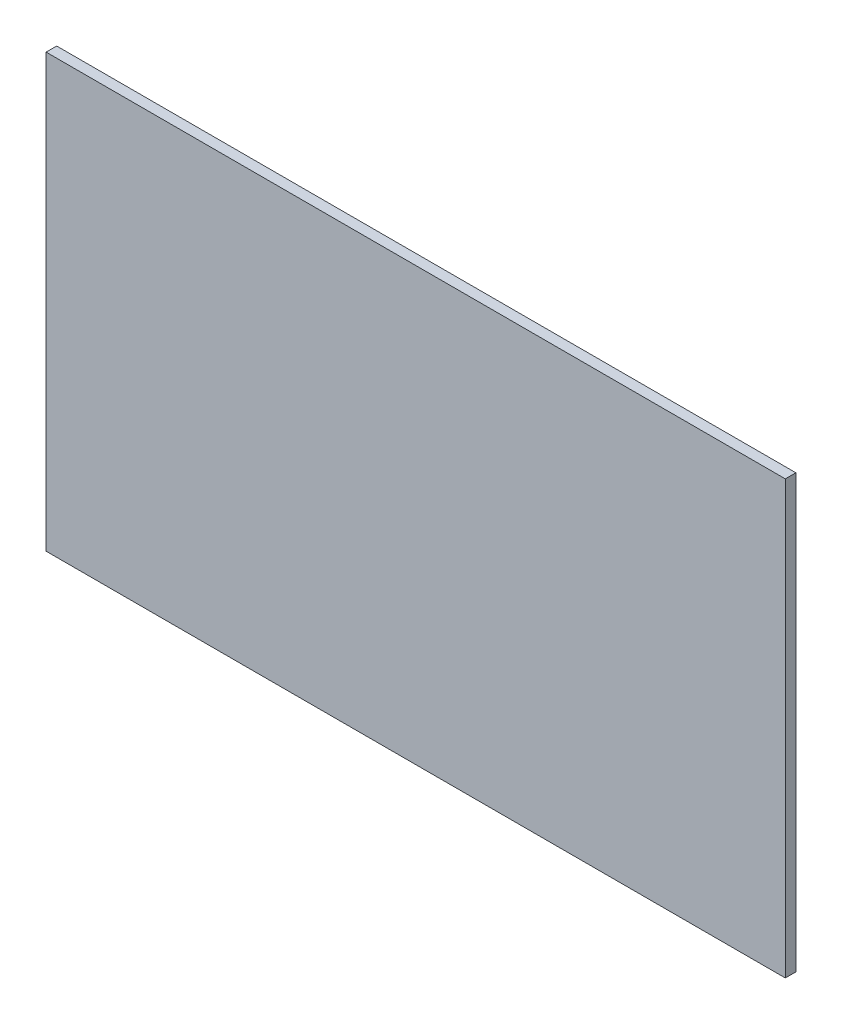
SolidWorks part; units mm, degrees
ref_plane "Front Plane" through (0, 0, 0) normal (0, 0, 1) x (1, 0, 0)
ref_plane "Top Plane" through (0, 0, 0) normal (0, 1, 0) x (1, 0, 0)
ref_plane "Right Plane" through (0, 0, 0) normal (1, 0, 0) x (0, 0, -1)
sketch "Sketch1" plane through (0, 0, 0) normal (0, 0, 1) x (1, 0, 0)
  line L1 (-136.2981, -74.7596) -> (1263.7019, -74.7596)
  line L2 (-136.2981, -74.7596) -> (-136.2981, 1325.2404)
  line L3 (-136.2981, 1325.2404) -> (1263.7019, 1325.2404)
  line L4 (1263.7019, -74.7596) -> (1263.7019, 1325.2404)
  point P4 (0, 0)
  point P5 (0, 0)
  point P6 (0, 0)
  point P7 (0, 0)
  point P8 (0, 0)
  dimension "D1" = 1400
  dimension "D2" = 1400
extrude "Boss-Extrude1" add sketch "Sketch1" along normal blind 20
sketch "Sketch3" plane through (0, 0, 0) normal (0, 0, -1) x (-1, 0, 0)
  line L0 (136.2981, 1325.2404) -> (136.2981, -74.7596) construction
  line L1 (-1263.7019, -74.7596) -> (136.2981, -74.7596)
  line L2 (-1263.7019, -74.7596) -> (-1263.7019, 506.5473)
  line L3 (-1263.7019, 506.5473) -> (136.2981, 506.5473)
  line L4 (136.2981, -74.7596) -> (136.2981, 506.5473)
extrude "Cut-Extrude1" cut sketch "Sketch3" against normal through all
